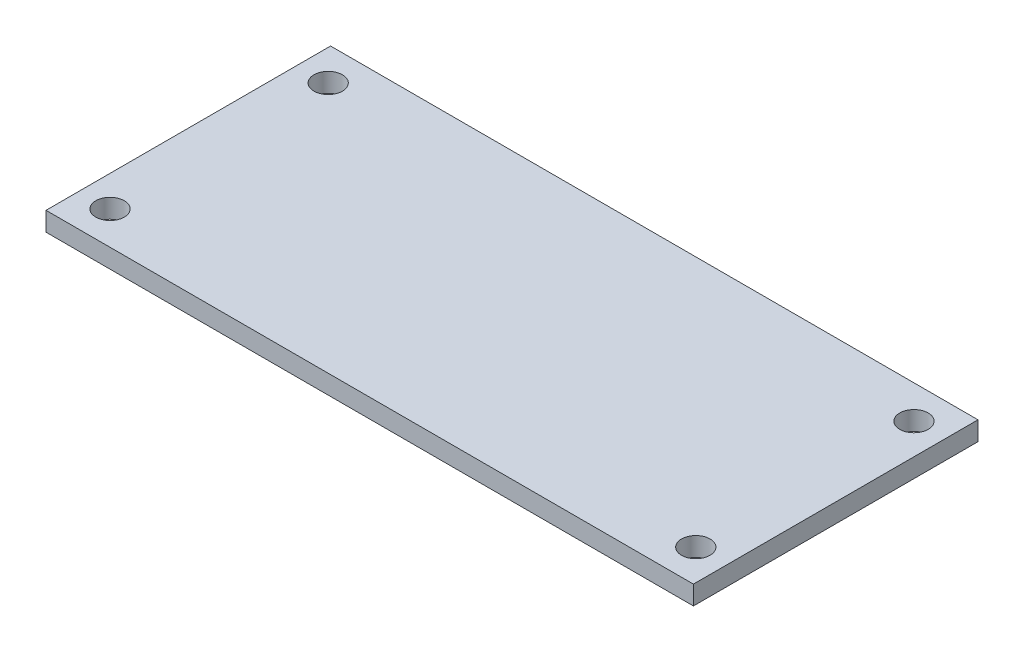
SolidWorks part; units mm, degrees
ref_plane "Front Plane" through (0, 0, 0) normal (0, 0, 1) x (1, 0, 0)
ref_plane "Top Plane" through (0, 0, 0) normal (0, 1, 0) x (1, 0, 0)
ref_plane "Right Plane" through (0, 0, 0) normal (1, 0, 0) x (0, 0, -1)
sketch "Sketch1" plane through (0, 0, 0) normal (0, 1, 0) x (1, 0, 0)
  line L1 (0, 0) -> (68.25, 0)
  line L2 (0, 0) -> (0, 30)
  line L3 (0, 30) -> (68.25, 30)
  line L4 (68.25, 0) -> (68.25, 30)
  line L8 (34.125, 26.5) -> (34.125, 30) construction
  line L9 (3.25, 26.5) -> (65, 26.5) construction
  line L10 (3.25, 26.5) -> (3.25, 3.5) construction
  line L11 (3.25, 3.5) -> (65, 3.5) construction
  line L12 (65, 26.5) -> (65, 3.5) construction
  line L14 (34.125, 3.5) -> (34.125, 0) construction
  line L16 (65, 15) -> (68.25, 15) construction
  line L18 (3.25, 15) -> (0, 15) construction
  circle A4 centre (3.25, 26.5) radius 1.5
  circle A5 centre (65, 3.5) radius 1.5
  circle A6 centre (65, 26.5) radius 1.5
  circle A7 centre (3.25, 3.5) radius 1.5
  dimension "D4" = 23
  dimension "D1" = 3
  dimension "D2" = 61.75
  dimension "D3" = 68.25
  dimension "D5" = 30
extrude "Boss-Extrude1" add sketch "Sketch1" along normal blind 2 contours L1 L4 L3 L2 A7 A6 A5 A4
